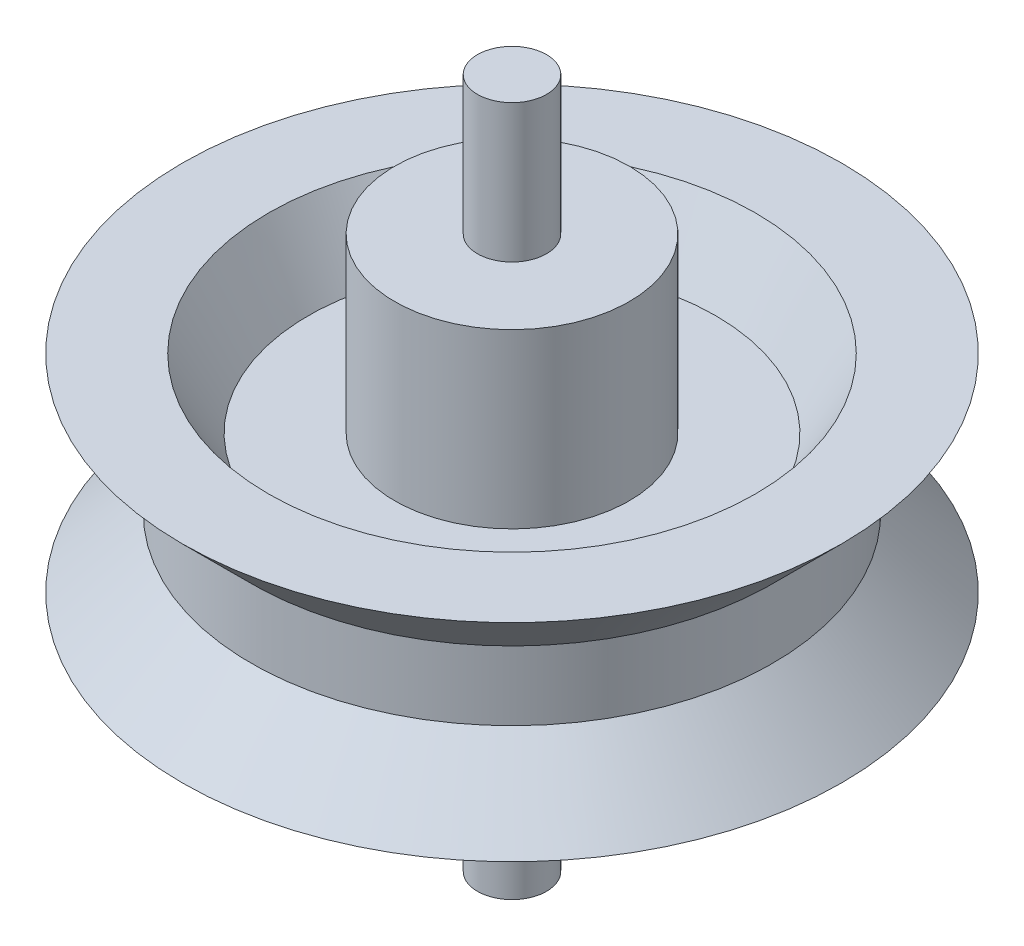
SolidWorks part; units mm, degrees
ref_plane "Plan de face" through (0, 0, 0) normal (0, 0, 1) x (1, 0, 0)
ref_plane "Plan de dessus" through (0, 0, 0) normal (0, 1, 0) x (1, 0, 0)
ref_plane "Plan de droite" through (0, 0, 0) normal (1, 0, 0) x (0, 0, -1)
sketch "Esquisse2" plane through (0, 0, 0) normal (1, 0, 0) x (0, 0, -1)
  line L0 (3.4, 0) -> (3.4, -5)
  line L1 (1, -5) -> (3.4, -5)
  line L2 (0, 0) -> (0, 15.5069) construction
  line L3 (1, 7) -> (1, 11)
  line L4 (1, 11) -> (0, 11)
  line L5 (0, 11) -> (0, -9)
  line L6 (0, -9) -> (1, -9)
  line L7 (1, -9) -> (1, -5)
  line L14 (3.4, 0) -> (5.9, 0)
  line L15 (5.9, 0) -> (7.0547, -2)
  line L16 (7.0547, -2) -> (9.5547, -2)
  line L17 (9.5547, -2) -> (7.5547, 0)
  line L18 (7.5547, 0) -> (7.5547, 2)
  line L19 (7.5547, 2) -> (9.5547, 4)
  line L20 (9.5547, 4) -> (7.0547, 4)
  line L21 (7.0547, 4) -> (5.9, 2)
  line L22 (5.9, 2) -> (3.4, 2)
  line L23 (3.4, 2) -> (3.4, 7)
  line L24 (3.4, 7) -> (1, 7)
  dimension "D1" = 135
  dimension "D2" = 135
  dimension "D3" = 120
  dimension "D4" = 120
  dimension "D5" = 2
  dimension "D6" = 2.5
  dimension "D7" = 2
  dimension "D8" = 5
  dimension "D9" = 2.5
  dimension "D10" = 2.4
  dimension "D11" = 20
  dimension "D12" = 5
  dimension "D13" = 2
  dimension "D14" = 12
  dimension "D15" = 2
  dimension "D16" = 2
  dimension "D17" = 2
  dimension "D18" = 5
  dimension "D19" = 9
  dimension "D20" = 4
  dimension "D21" = 4
  dimension "D22" = 1
revolve "Révolution1" add sketch "Esquisse2" angle 360 about L2
